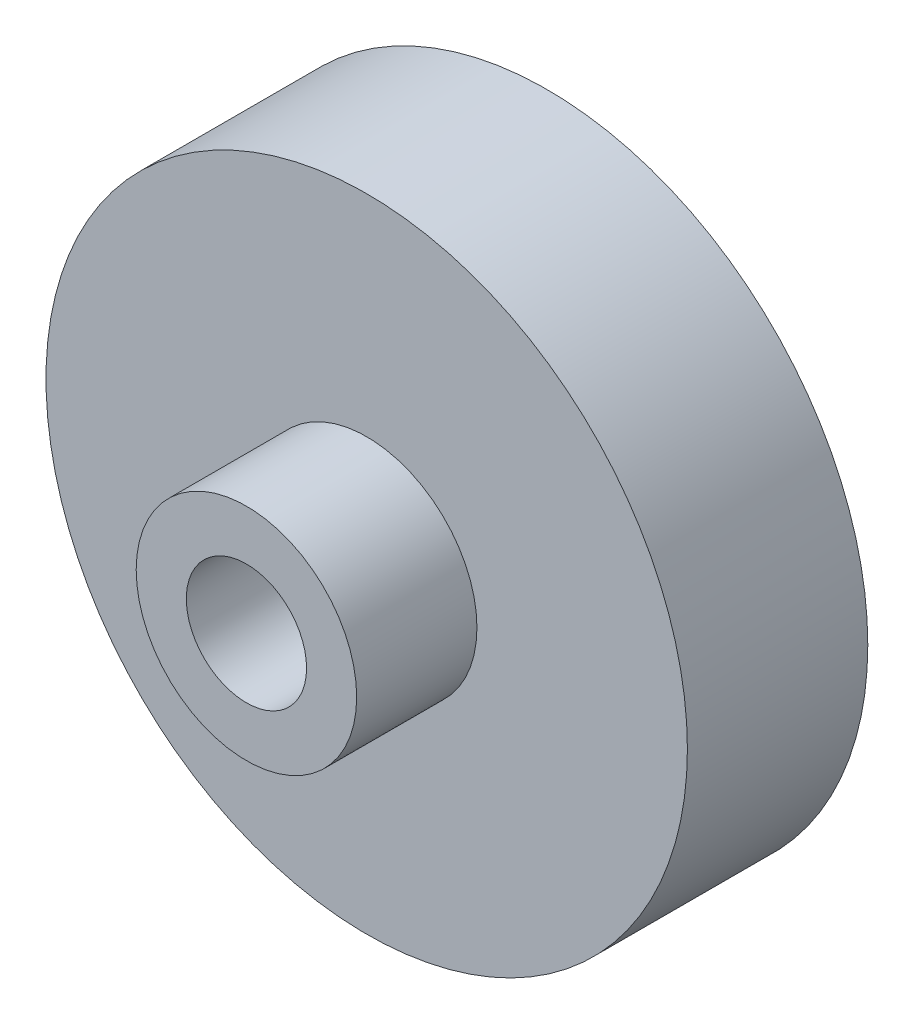
SolidWorks part; units mm, degrees
ref_plane "前视基准面" through (0, 0, 0) normal (0, 0, 1) x (1, 0, 0)
ref_plane "上视基准面" through (0, 0, 0) normal (0, 1, 0) x (1, 0, 0)
ref_plane "右视基准面" through (0, 0, 0) normal (1, 0, 0) x (0, 0, -1)
sketch "草图1" plane through (0, 0, 0) normal (0, 0, 1) x (1, 0, 0)
  circle A0 centre (0, 0) radius 16
extrude "凸台-拉伸1" add sketch "草图1" along normal blind 9
sketch "草图2" plane through (0, 0, 9) normal (0, 0, 1) x (1, 0, 0)
  circle A0 centre (0, 0) radius 6
extrude "凸台-拉伸2" add sketch "草图2" along normal blind 0.5
sketch "草图3" plane through (0, 0, 9.5) normal (0, 0, 1) x (1, 0, 0)
  circle A0 centre (0, 0) radius 16
extrude "凸台-拉伸3" add sketch "草图3" along normal blind 3.25
sketch "草图4" plane through (0, 0, 12.75) normal (0, 0, 1) x (1, 0, 0)
  circle A0 centre (0, 0) radius 5.5
extrude "凸台-拉伸4" add sketch "草图4" along normal blind 2.25
sketch "草图5" plane through (0, 0, 15) normal (0, 0, 1) x (1, 0, 0)
  circle A0 centre (0, 0) radius 3
extrude "切除-拉伸1" cut sketch "草图5" against normal blind 26.25
sketch "草图6" plane through (0, 0, 12.75) normal (0, 0, 1) x (1, 0, 0)
  circle A0 centre (0, 0) radius 5.5
  circle A1 centre (0, 0) radius 8
extrude "切除-拉伸2" cut sketch "草图6" against normal blind 2.25
sketch "草图7" plane through (0, 0, 0) normal (0, 0, -1) x (-1, 0, 0)
  circle A1 centre (8.6603, 5) radius 0.6
  circle A2 centre (-8.6603, 5) radius 0.6
  circle A3 centre (0, -10) radius 0.6
extrude "切除-拉伸3" cut sketch "草图7" against normal blind 6
sketch "草图8" plane through (0, 0, 12.75) normal (0, 0, 1) x (1, 0, 0)
  circle A2 centre (5, -8.6603) radius 0.6
  circle A3 centre (5, 8.6603) radius 0.6
  circle A4 centre (-10, 0) radius 0.6
extrude "切除-拉伸4" cut sketch "草图8" against normal blind 3
sketch "草图9" plane through (0, 0, 12.75) normal (0, 0, 1) x (1, 0, 0)
  circle A0 centre (0, 0) radius 5.5
  circle A1 centre (0, 0) radius 18.2908
extrude "切除-拉伸5" cut sketch "草图9" against normal blind 3.75
